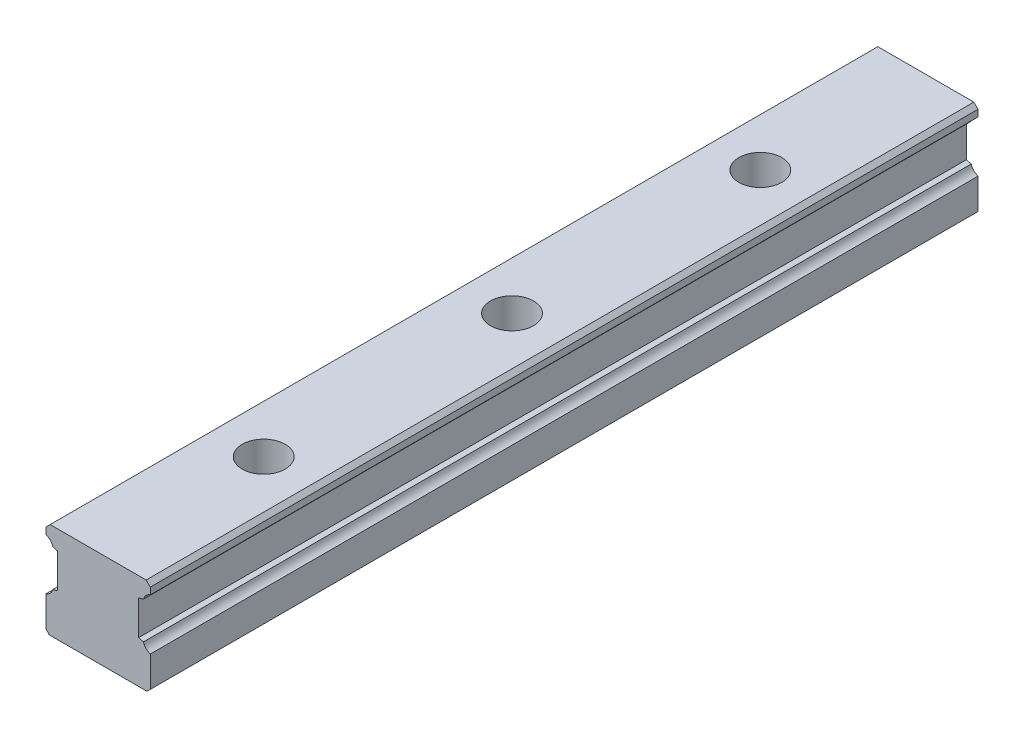
SolidWorks part; units mm, degrees
ref_plane "Plano frontal" through (0, 0, 0) normal (0, 0, 1) x (1, 0, 0)
ref_plane "Plano superior" through (0, 0, 0) normal (0, 1, 0) x (1, 0, 0)
ref_plane "Plano direito" through (0, 0, 0) normal (1, 0, 0) x (0, 0, -1)
sketch "Esboço1" plane through (0, 0, 0) normal (0, 0, 1) x (1, 0, 0)
  line L0 (-31.5, 20.5273) -> (-31.5, 0)
  line L1 (-31.5, 0) -> (31.5, 0)
  line L2 (31.5, 0) -> (31.5, 20.5273)
  line L3 (27.3973, 24.8216) -> (24.5, 25.5979)
  line L4 (24.5, 25.5979) -> (24.5, 46.3977)
  line L5 (24.5, 46.3977) -> (27.3971, 47.1739)
  line L6 (31.5, 51.4749) -> (31.5, 58)
  line L7 (31.5, 58) -> (-31.5, 58)
  line L8 (-31.5, 58) -> (-31.5, 51.4749)
  line L9 (-27.3978, 47.1758) -> (-24.5, 46.3997)
  line L10 (-24.5, 46.3997) -> (-24.5, 25.597)
  line L11 (-24.5, 25.597) -> (-27.3979, 24.8234)
  arc A0 (-27.3979, 24.8234) -> (-31.5, 20.5273) centre (-33.3777, 26.4267) cw
  arc A1 (31.5, 20.5273) -> (27.3973, 24.8216) centre (33.3765, 26.4271) cw
  arc A2 (27.3971, 47.1739) -> (31.5, 51.4749) centre (33.3782, 45.5757) cw
  arc A3 (-31.5, 51.4749) -> (-27.3978, 47.1758) centre (-33.3784, 45.5757) cw
extrude "Ressalto-extrusão1" add sketch "Esboço1" along normal blind 500
hole_wizard "Rebaixo para parafuso de cabeça sextavada de M161" positions "Esboço3" profile "Esboço2" counterbore size "M16" standard "Ansi Metric"
sketch "Esboço3" plane through (0, 58, 0) normal (0, 1, 0) x (1, 0, 0)
  line L0 (0, -100) -> (0, 0) construction
  line L1 (31.5, 0) -> (-31.5, 0) construction
  point P0 (0, -100)
  point P23 (0, -250)
  point P24 (0, -400)
  point P25 (0, -550)
  point P26 (0, -700)
  point P27 (0, -850)
  point P28 (0, -1000)
  point P29 (0, -1150)
  point P30 (0, -1300)
  point P31 (0, -1450)
  point P32 (0, -1600)
  point P33 (0, -1750)
  point P34 (0, -1900)
  point P35 (0, -2050)
  point P36 (0, -2200)
  point P37 (0, -2350)
  dimension "D1" = 100
  dimension "D2" = 16
sketch "Esboço2" plane through (0, 58, 100) normal (1, 0, 0) x (0, 0, 1)
  line L0 (0, 0) -> (0, 58)
  line L1 (0, 58) -> (9, 58)
  line L3 (9, 58) -> (9, 25)
  line L4 (9, 25) -> (13, 25)
  line L5 (13, 25) -> (13, 0)
  line L7 (13, 0) -> (0, 0)
  line L11 (0, -6.35) -> (0, 107.95) construction
  dimension "Thru Hole Dia." = 18
  dimension "Thru Hole Depth" = 58
  dimension "C'Bore Dia." = 26
  dimension "C'Bore Depth" = 25
chamfer "Chanfro1" distance 2.5003 angle 45 1 edges at (-31.5, 58, 250)
chamfer "Chanfro2" distance 2.5003 angle 45.002 1 edges at (31.5, 58, 250)
chamfer "Chanfro3" distance 2 angle 45 2 edges at (31.5, 0, 250) (-31.5, 0, 250)
